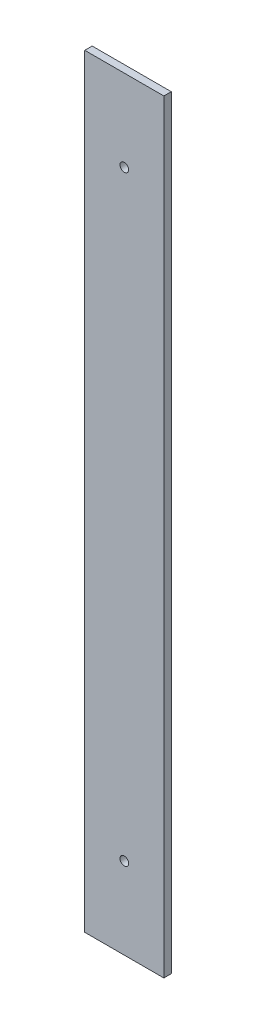
SolidWorks part; units mm, degrees
ref_plane "Plan de face" through (0, 0, 0) normal (0, 0, 1) x (1, 0, 0)
ref_plane "Plan de dessus" through (0, 0, 0) normal (0, 1, 0) x (1, 0, 0)
ref_plane "Plan de droite" through (0, 0, 0) normal (1, 0, 0) x (0, 0, -1)
sketch "Esquisse1" plane through (0, 0, 0) normal (0, 0, 1) x (1, 0, 0)
  line L0 (0, 154.5) -> (0, -154.5) construction
  line L1 (16, 154.5) -> (-16, 154.5)
  line L2 (16, 154.5) -> (16, -154.5)
  line L3 (16, -154.5) -> (-16, -154.5)
  line L4 (-16, 154.5) -> (-16, -154.5)
  line L5 (16, 154.5) -> (-16, -154.5) construction
  line L6 (16, -154.5) -> (-16, 154.5) construction
  line L7 (-16, 0) -> (16, 0) construction
  circle A0 centre (0, 121.5) radius 1.75
  circle A1 centre (0, -121.5) radius 1.75
  point P0 (0, 0)
  dimension "D3" = 3.5
  dimension "D1" = 32
  dimension "D2" = 309
  dimension "D4" = 33
extrude "Boss.-Extru.1" add sketch "Esquisse1" along normal blind 3
